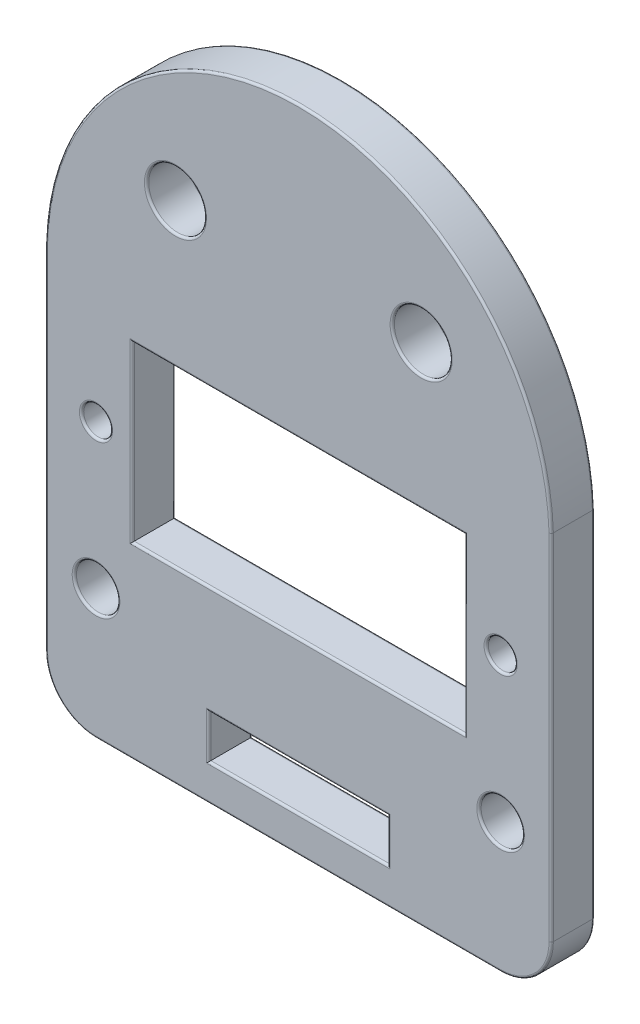
SolidWorks part; units mm, degrees
material "Balsa"
ref_plane "Front Plane" through (0, 0, 0) normal (0, 0, 1) x (1, 0, 0)
ref_plane "Top Plane" through (0, 0, 0) normal (0, 1, 0) x (1, 0, 0)
ref_plane "Right Plane" through (0, 0, 0) normal (1, 0, 0) x (0, 0, -1)
sketch "Sketch1" plane through (0, 0, 0) normal (0, 0, 1) x (1, 0, 0)
  line L0 (0, -19) -> (0, 26) construction
  line L1 (11.5, -6) -> (-11.5, -6)
  line L2 (11.5, -6) -> (11.5, 6)
  line L3 (11.5, 6) -> (-11.5, 6)
  line L4 (-11.5, -6) -> (-11.5, 6)
  line L5 (11.5, -6) -> (-11.5, 6) construction
  line L6 (11.5, 6) -> (-11.5, -6) construction
  line L7 (-6.2, -15) -> (6.2, -15) construction
  line L8 (-6.2, -13.5) -> (6.2, -13.5)
  line L9 (-6.2, -16.5) -> (6.2, -16.5)
  line L10 (6.2, -13.5) -> (6.2, -16.5)
  line L11 (-17.5, 9) -> (17.5, 9) construction
  line L12 (-17.5, 9) -> (-17.5, -19)
  line L13 (-17.5, -19) -> (17.5, -19)
  line L14 (17.5, 9) -> (17.5, -19)
  line L15 (-6.2, -13.5) -> (-6.2, -16.5)
  circle A0 centre (-14, 0) radius 1
  circle A1 centre (-14, -10) radius 1.5
  circle A4 centre (-8.5, 16) radius 2
  circle A5 centre (14, -10) radius 1.5
  circle A6 centre (14, 0) radius 1
  circle A7 centre (8.5, 16) radius 2
  arc A8 (-17.5, 9) -> (17.5, 9) centre (0, 8.4926) cw
  point P0 (0, 0)
  point P10 (-11.5, 0)
  point P11 (0, -15)
  point P33 (0, 26)
  dimension "D5" = 2
  dimension "D7" = 3
  dimension "D12" = 10
  dimension "D13" = 4
  dimension "D1" = 23
  dimension "D2" = 12
  dimension "D3" = 45
  dimension "D4" = 13
  dimension "D6" = 2.5
  dimension "D8" = 10
  dimension "D10" = 12.4
  dimension "D11" = 4
  dimension "D14" = 8.5
  dimension "D15" = 28
  dimension "D16" = 35
  dimension "D17" = 13
extrude "Boss-Extrude1" add sketch "Sketch1" along normal blind 3
fillet "Fillet1" radius 3.5 2 edges at (17.5, -19, 1.5) (-17.5, -19, 1.5)
fillet "Fillet2" radius 0.15 40 edges at (6.5, 16, 0) (12.5, -10, 0) (0, -16.5, 0) (0, -13.5, 0) (-12.5, -10, 0) (11.5, 0, 0) (0, -6, 0) (-11.5, 0, 0) (0, 6, 0) (0, 26, 0) (-17.5, -3.25, 0) (-16.4749, -17.9749, 0) (0, -19, 0) (16.4749, -17.9749, 0) (17.5, -3.25, 0) (-13, 0, 0) (-6.5, 16, 0) (13, 0, 0) (6.5, 16, 3) (13, 0, 3) (12.5, -10, 3) (-6.5, 16, 3) (0, -16.5, 3) (0, -13.5, 3) (-16.4749, -17.9749, 3) (-17.5, -3.25, 3) (0, 26, 3) (17.5, -3.25, 3) (16.4749, -17.9749, 3) (0, -19, 3) (0, -6, 3) (11.5, 0, 3) (0, 6, 3) (-11.5, 0, 3) (-13, 0, 3) (-12.5, -10, 3) (6.2, -15, 0) (-6.2, -15, 0) (6.2, -15, 3) (-6.2, -15, 3)
